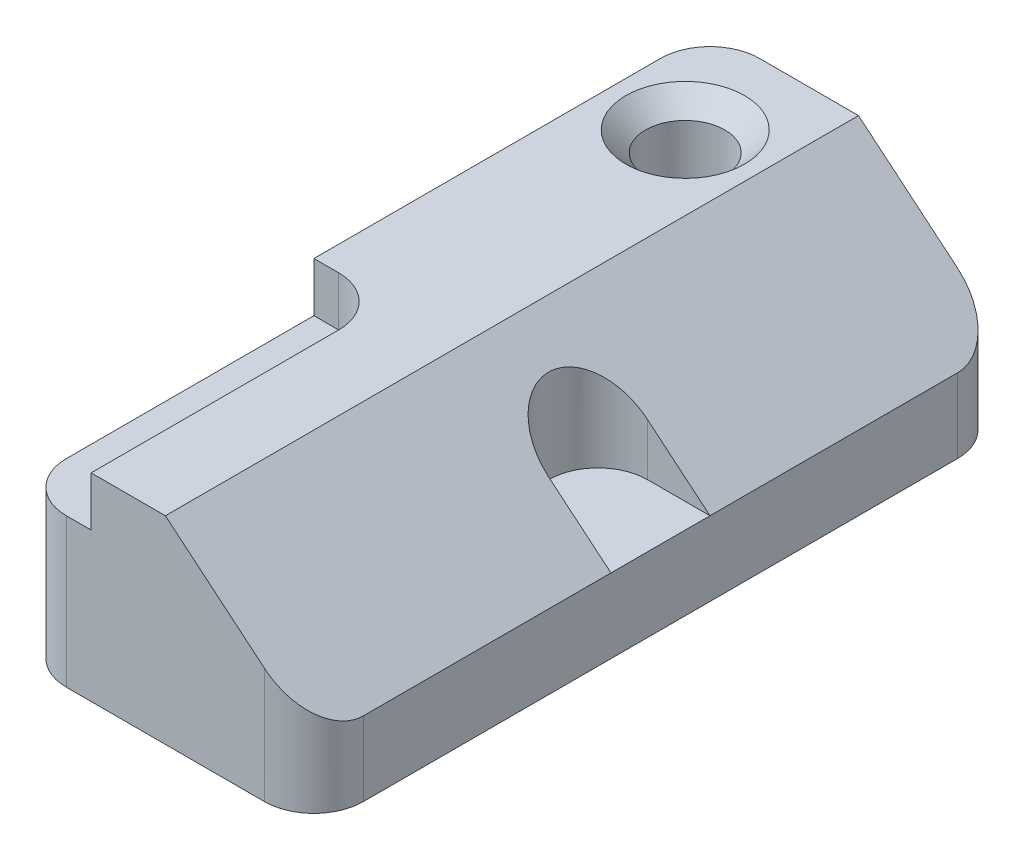
SolidWorks part; units mm, degrees
material "Plain Carbon Steel"
ref_plane "Front Plane" through (0, 0, 0) normal (0, 0, 1) x (1, 0, 0)
ref_plane "Top Plane" through (0, 0, 0) normal (0, 1, 0) x (1, 0, 0)
ref_plane "Right Plane" through (0, 0, 0) normal (1, 0, 0) x (0, 0, -1)
sketch "Sketch1" plane through (0, 0, 0) normal (0, 0, 1) x (1, 0, 0)
  line L0 (0, 0) -> (76.2, 0)
  line L1 (76.2, 0) -> (76.2, 19.05)
  line L2 (0, 0) -> (0, 50.8)
  line L3 (0, 50.8) -> (38.1, 50.8)
  line L4 (38.1, 50.8) -> (76.2, 19.05)
  dimension "D1" = 76.2
  dimension "D2" = 19.05
  dimension "D3" = 50.8
  dimension "D4" = 38.1
extrude "Boss-Extrude1" add sketch "Sketch1" along normal blind 177.8
sketch "Sketch2" plane through (0, 50.8, 0) normal (0, 1, 0) x (1, 0, 0)
  line L0 (0, 0) -> (19.05, 0)
  line L1 (38.1, 0) -> (0, 0) construction
  line L2 (0, 0) -> (0, -25.4)
  line L3 (0, -177.8) -> (0, 0) construction
  line L4 (0, -25.4) -> (19.05, -25.4) construction
  line L5 (19.05, 0) -> (19.05, -25.4) construction
  circle A0 centre (19.05, -25.4) radius 10.16
  dimension "D3" = 20.32
  dimension "D1" = 19.05
  dimension "D2" = 25.4
extrude "Cut-Extrude1" cut sketch "Sketch2" against normal through all contours A0
chamfer "Chamfer1" distance 5.08 angle 45 1 edges at (19.05, 50.8, 35.56)
sketch "Sketch3" plane through (0, 50.8, 0) normal (0, 1, 0) x (1, 0, 0)
  line L1 (0, -177.8) -> (19.05, -177.8)
  line L2 (0, -177.8) -> (0, -101.6)
  line L3 (0, -101.6) -> (19.05, -101.6)
  line L4 (19.05, -177.8) -> (19.05, -101.6)
  dimension "D1" = 19.05
  dimension "D2" = 76.2
extrude "Cut-Extrude2" cut sketch "Sketch3" against normal blind 12.7 contours L2 L1 L4 L3
fillet "Fillet1" radius 12.7 1 edges at (19.05, 44.45, 101.6)
fillet "Fillet2" radius 12.7 4 edges at (0, 19.05, 177.8) (0, 25.4, 0) (76.2, 9.525, 0) (76.2, 9.525, 177.8)
sketch "Sketch17" plane through (0, 50.8, 0) normal (0, 1, 0) x (1, 0, 0)
  line L0 (76.2, -76.2) -> (60.198, -76.2)
  line L1 (76.2, -165.1) -> (76.2, -12.7) construction
  line L2 (60.198, -101.6) -> (76.2, -101.6)
  line L3 (76.2, -101.6) -> (76.2, -76.2)
  arc A0 (60.198, -76.2) -> (60.198, -101.6) centre (60.198, -88.9) ccw
  point P6 (76.2, -88.9)
  dimension "D2" = 12.7
  dimension "D1" = 16.002
extrude "Cut-Extrude8" cut sketch "Sketch17" against normal up to vertex (31.75 mm away)
